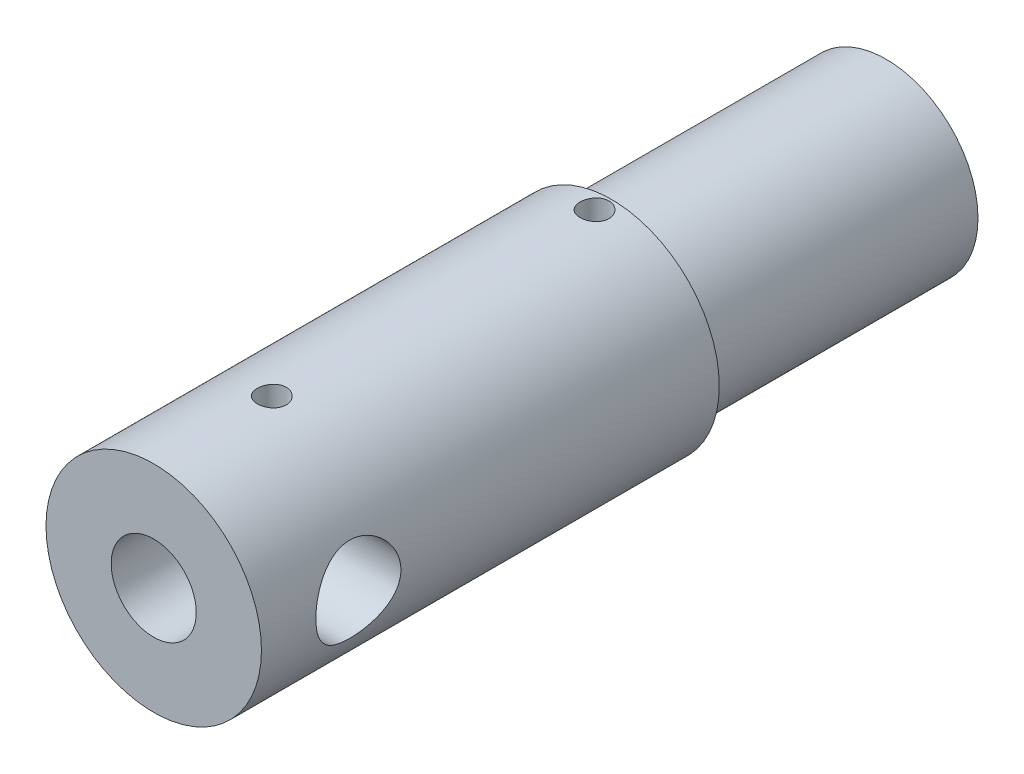
SolidWorks part; units mm, degrees
material "6061 Alloy"
ref_plane "Front Plane" through (0, 0, 0) normal (0, 0, 1) x (1, 0, 0)
ref_plane "Top Plane" through (0, 0, 0) normal (0, 1, 0) x (1, 0, 0)
ref_plane "Right Plane" through (0, 0, 0) normal (1, 0, 0) x (0, 0, -1)
sketch "Sketch1" plane through (0, 0, 0) normal (0, 0, 1) x (1, 0, 0)
  circle A0 centre (0, 0) radius 10.8204
  circle A2 centre (0, 0) radius 8.7122
extrude "Extrude1" add sketch "Sketch1" along normal blind 86.36 contours A0 A2
sketch "Sketch2" plane through (0, 0, 86.36) normal (0, 0, 1) x (1, 0, 0)
  circle A0 centre (0, 0) radius 12.7
  circle A1 centre (0, 0) radius 2.5908
extrude "Extrude2" add sketch "Sketch2" against normal blind 53.975
sketch "Sketch3" plane through (0, 0, 0) normal (0, 0, -1) x (-1, 0, 0)
  circle A0 centre (0, 0) radius 6.5151
  circle A1 centre (0, 0) radius 8.7122
extrude "Extrude3" add sketch "Sketch3" against normal blind 35.3822
sketch "Sketch4" plane through (0, 0, 0) normal (0, 0, -1) x (-1, 0, 0)
  circle A0 centre (0, 0) radius 8.7122
  circle A1 centre (0, 0) radius 6.5151
extrude "Cut-Extrude1" cut sketch "Sketch4" against normal blind 2.3876
ref_plane "Plane2" through (0, -12.7, 0) normal (0, 1, 0) x (-1, 0, 0)
sketch "Sketch15" plane through (0, -12.7, 0) normal (0, 1, 0) x (-1, 0, 0)
  line L0 (0, 0) -> (0, 38.8874)
  circle A0 centre (0, 38.8874) radius 2.3622
extrude "Cut-Extrude5" cut sketch "Sketch15" along normal blind 7.2644 contours A0
ref_plane "Plane3" through (0, 12.7, 0) normal (0, 1, 0) x (-1, 0, 0)
sketch "Sketch17" plane through (0, 12.7, 0) normal (0, 1, 0) x (-1, 0, 0)
  line L0 (0, 0) -> (0, 34.3916)
  line L1 (0, 0) -> (0, 72.4408)
  circle A0 centre (0, 34.3916) radius 1.7018
  circle A1 centre (0, 72.4408) radius 1.7018
extrude "Cut-Extrude6" cut sketch "Sketch17" against normal blind 4.572
sketch "Sketch18" plane through (0, 0, 86.36) normal (0, 0, 1) x (1, 0, 0)
  circle A0 centre (0, 0) radius 5.0165
extrude "Cut-Extrude7" cut sketch "Sketch18" against normal blind 8.382
ref_plane "Plane4" through (12.7, 0, 0) normal (1, 0, 0) x (0, 0, -1)
sketch "Sketch19" plane through (12.7, 0, 0) normal (1, 0, 0) x (0, 0, -1)
  line L0 (0, 0) -> (-74.93, 0)
  circle A0 centre (-74.93, 0) radius 5.0165
extrude "Cut-Extrude8" cut sketch "Sketch19" against normal blind 8.382
